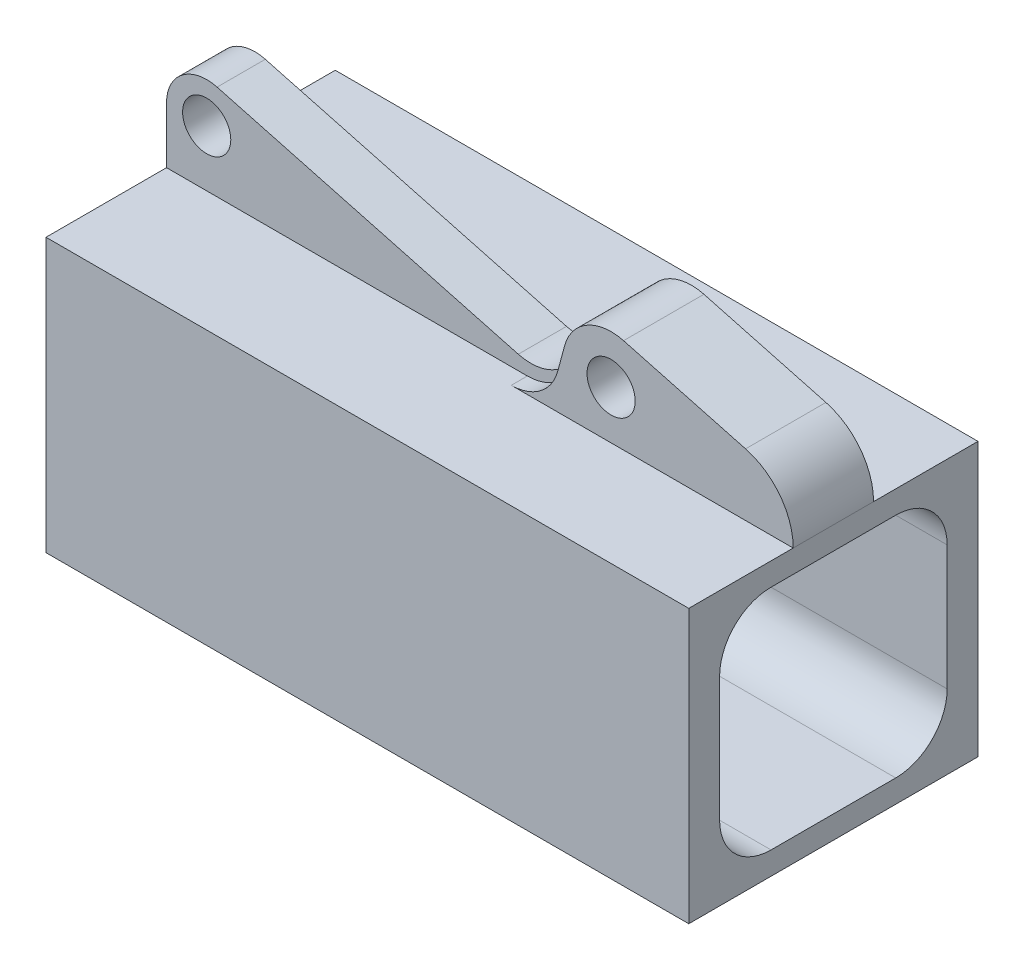
SolidWorks part; units mm, degrees
material "6061-T6 (SS)"
ref_plane "Front Plane" through (0, 0, 0) normal (0, 0, 1) x (1, 0, 0)
ref_plane "Top Plane" through (0, 0, 0) normal (0, 1, 0) x (1, 0, 0)
ref_plane "Right Plane" through (0, 0, 0) normal (1, 0, 0) x (0, 0, -1)
sketch "Sketch1" plane through (0, 0, 0) normal (1, 0, 0) x (0, 0, -1)
  line L1 (-11.2395, 11.2395) -> (11.2395, 11.2395)
  line L2 (-11.2395, 11.2395) -> (-11.2395, -11.2395)
  line L3 (-11.2395, -11.2395) -> (11.2395, -11.2395)
  line L4 (11.2395, 11.2395) -> (11.2395, -11.2395)
  line L5 (-11.2395, 11.2395) -> (11.2395, -11.2395) construction
  line L6 (-11.2395, -11.2395) -> (11.2395, 11.2395) construction
  line L7 (-14.2875, 13.4938) -> (14.2875, 13.4938)
  line L8 (-14.2875, 13.4938) -> (-14.2875, -13.4937)
  line L9 (-14.2875, -13.4937) -> (14.2875, -13.4937)
  line L10 (14.2875, 13.4938) -> (14.2875, -13.4937)
  line L11 (-14.2875, 13.4938) -> (14.2875, -13.4937) construction
  line L12 (-14.2875, -13.4937) -> (14.2875, 13.4938) construction
  point P0 (0, 0)
  point P6 (0, 0)
  dimension "D1" = 26.9875
  dimension "D2" = 22.479
  dimension "D3" = 28.575
extrude "Boss-Extrude1" add sketch "Sketch1" along normal mid plane 63.5
fillet "Fillet1" radius 5.08 4 edges at (0, -11.2395, 11.2395) (0, 11.2395, 11.2395) (0, 11.2395, -11.2395) (0, -11.2395, -11.2395)
sketch "Sketch2" plane through (0, 0, 0) normal (0, 0, 1) x (1, 0, 0)
  line L0 (7.5531, 13.4938) -> (9.1595, 19.4889)
  line L1 (31.75, 13.4938) -> (-31.75, 13.4938) construction
  line L3 (14.9924, 22.8565) -> (27.0435, 19.6274)
  line L4 (31.75, 13.4938) -> (7.5531, 13.4938)
  line L5 (13.7597, 23.0187) -> (-11.3118, 23.0187) construction
  line L6 (31.75, -13.4937) -> (-31.75, -13.4937) construction
  line L9 (31.75, 13.4938) -> (31.75, -13.4937) construction
  circle A0 centre (13.7597, 18.2562) radius 2.3813
  arc A1 (9.1595, 19.4889) -> (14.9924, 22.8565) centre (13.7597, 18.2562) cw
  arc A2 (31.75, 13.4938) -> (27.0435, 19.6274) centre (25.4, 13.4937) ccw
  point P7 (33.7072, 18.0781)
  point P11 (0, 0)
  point P14 (0, 0)
  point P21 (0, 0)
  dimension "D1" = 4.7625
  dimension "D2" = 4.7625
  dimension "D6" = 6.35
  dimension "D3" = 4.7625
  dimension "D4" = 15
  dimension "D5" = 36.5125
extrude "Boss-Extrude2" add sketch "Sketch2" along normal mid plane 7.9375
sketch "Sketch3" plane through (0, 0, 0) normal (0, 0, 1) x (1, 0, 0)
  line L0 (-31.75, 13.4938) -> (-31.75, 19.05)
  line L2 (-26.7541, 22.8835) -> (7.6024, 13.6777)
  line L4 (7.5531, 13.4938) -> (-31.75, 13.4938)
  line L5 (13.7597, 23.0187) -> (-27.7813, 23.0187) construction
  line L6 (27.0435, 19.6274) -> (14.9924, 22.8565) construction
  line L9 (7.6024, 13.6777) -> (7.5531, 13.4938)
  line L10 (9.1595, 19.4889) -> (7.5531, 13.4938) construction
  arc A0 (-31.75, 19.05) -> (-26.7541, 22.8835) centre (-27.7813, 19.05) cw
  circle A1 centre (-27.7813, 19.05) radius 2.3813
  circle A2 centre (13.7597, 18.2562) radius 2.3813 construction
  arc A5 (14.9924, 22.8565) -> (9.1595, 19.4889) centre (13.7597, 18.2562) ccw construction
  arc A6 (14.9924, 22.8565) -> (9.1595, 19.4889) centre (13.7597, 18.2562) ccw
  dimension "D1" = 5.5562
extrude "Boss-Extrude3" add sketch "Sketch3" along normal mid plane 4.7625 contours A0 L0 L4 L9 L2 A1
fillet "Fillet2" radius 4.7625 1 edges at (7.6024, 13.6777, 0)
fillet "Fillet3" radius 4.7625 2 edges at (7.5531, 13.4938, -3.175) (7.5531, 13.4938, 3.175)
